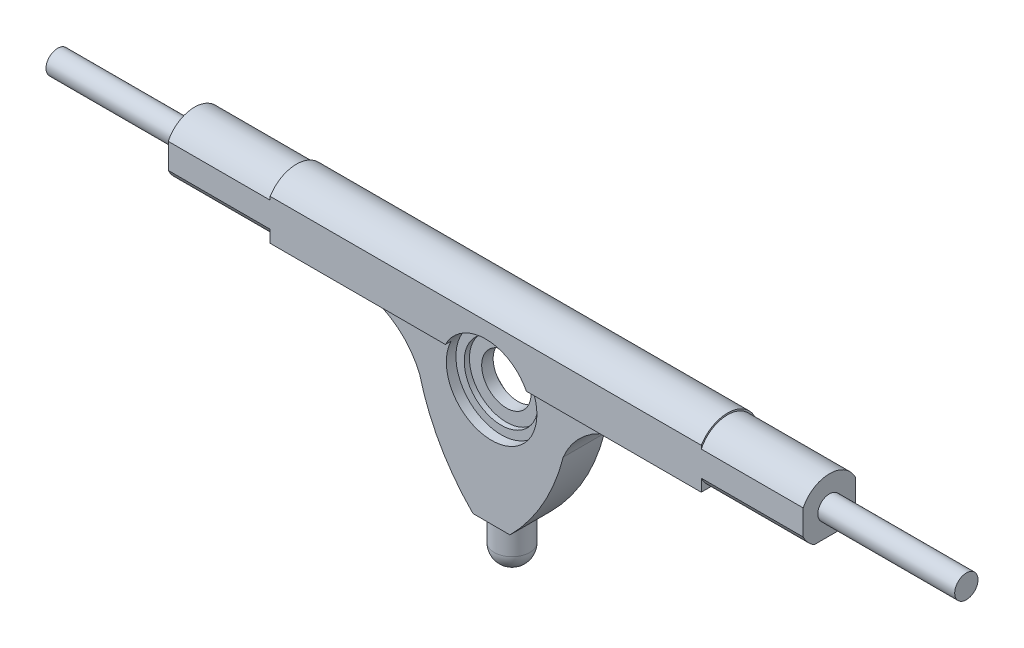
SolidWorks part; units mm, degrees
ref_plane "Front Plane" through (0, 0, 0) normal (0, 0, 1) x (1, 0, 0)
ref_plane "Top Plane" through (0, 0, 0) normal (0, 1, 0) x (1, 0, 0)
ref_plane "Right Plane" through (0, 0, 0) normal (1, 0, 0) x (0, 0, -1)
sketch "Sketch1" plane through (0, 0, 0) normal (1, 0, 0) x (0, 0, -1)
  line L1 (-9.017, -6.985) -> (9.017, -6.985)
  line L2 (-9.017, -6.985) -> (-9.017, 6.985)
  line L4 (9.017, -6.985) -> (9.017, 6.985)
  line L5 (-9.017, -6.985) -> (9.017, 6.985) construction
  line L6 (-9.017, 6.985) -> (9.017, -6.985) construction
  arc A0 (-9.017, 6.985) -> (9.017, 6.985) centre (0, 1.5224) cw
  point P0 (0, 0)
  point P7 (0, 12.065)
  dimension "D1" = 19.05
  dimension "D2" = 13.97
  dimension "D3" = 18.034
extrude "Boss-Extrude1" add sketch "Sketch1" along normal mid plane 218
sketch3d "3DSketch1"
  line L0 (0, -6.985, 0) -> (0, -54.483, 0) construction
  line L1 (-24.638, -22.225, 0) -> (0, -22.225, 0) construction
  line L2 (6.35, -54.483, 0) -> (-6.35, -54.483, 0)
  line L3 (-43.18, -6.985, 0) -> (43.18, -6.985, 0)
  arc A0 (-43.18, -6.985, 0) -> (-24.638, -22.225, 0) centre (-48.1235, -31.8993, 0) cw
  arc A1 (-24.638, -22.225, 0) -> (-6.35, -54.483, 0) centre (43.0905, -5.1407, 0) cw
  arc A2 (24.638, -22.225, 0) -> (6.35, -54.483, 0) centre (-43.0905, -5.1407, 0) ccw
  arc A3 (43.18, -6.985, 0) -> (24.638, -22.225, 0) centre (48.1235, -31.8993, 0) ccw
  point P7 (-48.1235, -31.8993, -25.4)
  point P10 (43.0905, -5.1407, 69.85)
  point P15 (-43.0905, -5.1407, -69.85)
  point P18 (48.1235, -31.8993, 25.4)
  dimension "D5" = 25.4
  dimension "D6" = 69.85
  dimension "D1" = 24.638
  dimension "D2" = 47.498
  dimension "D3" = 15.24
  dimension "D4" = 43.18
  dimension "D7" = 6.35
extrude "Boss-Extrude2" add sketch "3DSketch1" along direction (0, 0, -1) on the side of the normal mid plane 14.097
ref_plane "Plane1" through (0, 0, 0) normal (0, 0, 1) x (1, 0, 0)
sketch "Sketch8" plane through (0, 0, 0) normal (0, 0, 1) x (1, 0, 0)
  line L0 (0, -69.469) -> (0, -54.483)
  line L1 (-6.35, -54.483) -> (6.35, -54.483) construction
  line L2 (0, -54.483) -> (6.096, -54.483)
  line L3 (6.096, -54.483) -> (6.096, -63.373)
  line L4 (0, -47.1342) -> (0, -77.1544) construction
  arc A0 (6.096, -63.373) -> (0, -69.469) centre (0, -63.373) cw
  dimension "D1" = 8.89
  dimension "D2" = 6.096
revolve "Revolve2" add sketch "Sketch8" angle 360 about L4
sketch "Sketch9" plane through (0, 0, 7.0485) normal (0, 0, 1) x (1, 0, 0)
  circle A0 centre (0.0506, -13.9773) radius 4.6736
ref_plane "Plane2" through (0, -13.9773, 0) normal (0, -1, 0) x (-1, 0, 0)
sketch "Sketch10" plane through (0, -13.9773, 0) normal (0, -1, 0) x (-1, 0, 0)
  line L0 (-0.0506, -55.7699) -> (-0.0506, 64.4216) construction
  line L1 (-0.0506, -9.017) -> (-0.0506, 9.017)
  line L2 (19.1976, 0) -> (-22.9025, 0) construction
  line L4 (-0.0506, 9.017) -> (-15.6081, 9.017)
  line L5 (-15.6081, 9.017) -> (-15.6081, 3.7465)
  line L6 (-15.6081, 3.7465) -> (-12.7506, 3.7465)
  line L7 (-12.7506, 3.7465) -> (-12.7506, 1.9685)
  line L8 (-12.7506, 1.9685) -> (-8.5342, 1.9685)
  line L9 (-8.5342, 1.9685) -> (-8.5342, -1.9685)
  line L10 (-64.6711, 0) -> (64.6711, 0) construction
  line L12 (-0.0506, -9.017) -> (-15.6081, -9.017)
  line L13 (-15.6081, -9.017) -> (-15.6081, -3.7465)
  line L14 (-15.6081, -3.7465) -> (-12.7506, -3.7465)
  line L15 (-12.7506, -3.7465) -> (-12.7506, -1.9685)
  line L16 (-12.7506, -1.9685) -> (-8.5342, -1.9685)
  line L17 (-109, 9.017) -> (109, 9.017) construction
  point P5 (-0.0506, 0)
  point P23 (-8.5342, 0)
  dimension "D3" = 15.5575
  dimension "D4" = 12.7
  dimension "D5" = 8.4836
revolve "Cut-Revolve1" cut sketch "Sketch10" angle 360 about L0
sketch "Sketch11" plane through (109, 0, 0) normal (1, 0, 0) x (0, 0, -1)
  circle A0 centre (0, 1.5224) radius 4
  arc A1 (9.017, 6.985) -> (-9.017, 6.985) centre (0, 1.5224) ccw construction
  dimension "D1" = 8
extrude "Boss-Extrude3" add sketch "Sketch11" along normal blind 47
mirror "Mirror1" about plane through (0, 0, 0) normal (1, 0, 0) of "Boss-Extrude3"
sketch "Sketch12" plane through (109, 0, 0) normal (1, 0, 0) x (0, 0, -1)
  circle A0 centre (0, 1.5224) radius 10
  arc A1 (9.017, 6.985) -> (-9.017, 6.985) centre (0, 1.5224) ccw construction
  dimension "D1" = 20
extrude "Cut-Extrude1" cut sketch "Sketch12" against normal blind 35 flip side to cut
mirror "Mirror3" about plane through (0, 0, 0) normal (1, 0, 0) of "Cut-Extrude1"
